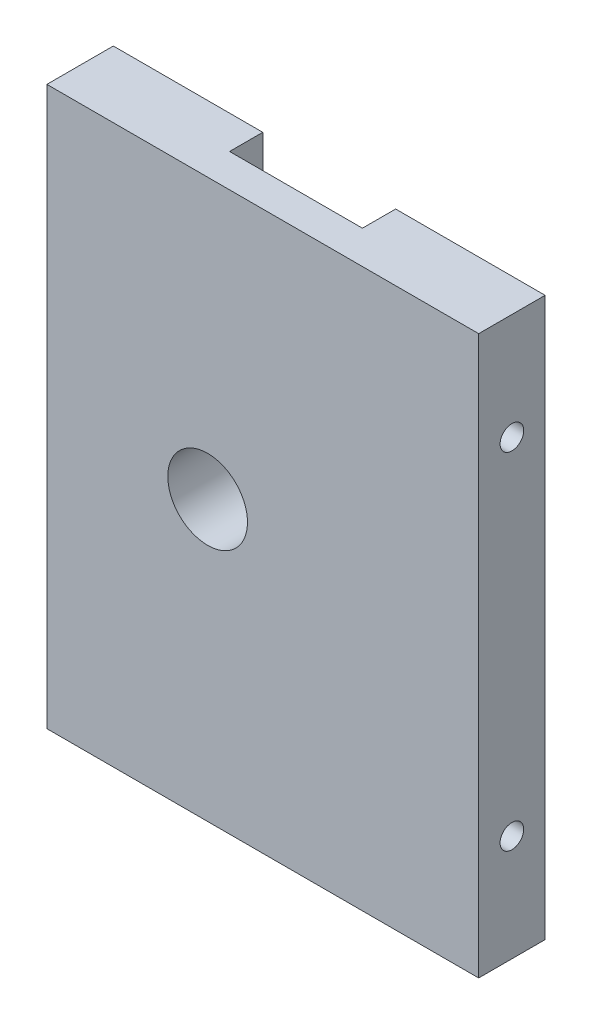
SolidWorks part; units mm, degrees
ref_plane "Front Plane" through (0, 0, 0) normal (0, 0, 1) x (1, 0, 0)
ref_plane "Top Plane" through (0, 0, 0) normal (0, 1, 0) x (1, 0, 0)
ref_plane "Right Plane" through (0, 0, 0) normal (1, 0, 0) x (0, 0, -1)
sketch "Sketch1" plane through (0, 0, 0) normal (0, 0, 1) x (1, 0, 0)
  line L1 (0, 0) -> (32.5, 0)
  line L2 (0, 0) -> (0, 42)
  line L3 (0, 42) -> (32.5, 42)
  line L4 (32.5, 0) -> (32.5, 42)
extrude "Boss-Extrude2" add sketch "Sketch1" along normal blind 5
sketch "Sketch2" plane through (0, 0, 5) normal (0, 0, 1) x (1, 0, 0)
  line L0 (0, 42) -> (0, 34)
  line L1 (0, 42) -> (0, 0) construction
  line L2 (0, 34) -> (32.5, 34)
  line L3 (32.5, 0) -> (32.5, 42) construction
  line L4 (0, 0) -> (0, 8)
  line L5 (0, 8) -> (32.5, 8)
sketch "Sketch3" plane through (0, 0, 0) normal (-1, 0, 0) x (0, 0, 1)
  line L0 (5, 34) -> (0, 34)
  line L1 (5, 42) -> (5, 34) construction
  line L2 (0, 42) -> (0, 0) construction
  line L3 (5, 8) -> (0, 8)
  line L4 (5, 0) -> (5, 8) construction
  line L5 (5, 42) -> (5, 0) construction
hole_wizard "#2-56 Tapped Hole1" positions "Sketch4" profile "Sketch5" tap size "#2-56" standard "ANSI Inch"
sketch "Sketch4" plane through (0, 0, 0) normal (-1, 0, 0) x (0, 0, 1)
  line L0 (5, 34) -> (0, 34) construction
  line L1 (5, 8) -> (0, 8) construction
  point P0 (2.5, 34)
  point P4 (2.5, 8)
sketch "Sketch5" plane through (0, 34, 2.5) normal (0, 1, 0) x (0, 0, 1)
  line L0 (0, 0) -> (0, 8)
  line L1 (0, 8) -> (0.889, 7.4658)
  line L2 (0.889, 7.4658) -> (0.889, 0)
  line L5 (0.889, 0) -> (0, 0)
  line L10 (0, 8) -> (-0.889, 7.4658) construction
  line L11 (0, -6.35) -> (0, 107.95) construction
  dimension "Tap Drill Dia." = 1.778
  dimension "Tap Drill Depth" = 8
  dimension "Drill Angle" = 118
cosmetic thread "Hole Thread1" parameters "D1"=4.37, "D2"=2.1844
cosmetic thread "Hole Thread2" parameters "D1"=4.37, "D2"=2.1844
sketch "Sketch6" plane through (32.5, 0, 0) normal (1, 0, 0) x (0, 0, -1)
  line L0 (-5, 34) -> (0, 34)
  line L1 (-5, 8) -> (0, 8)
hole_wizard "#2-56 Tapped Hole2" positions "Sketch7" profile "Sketch8" tap size "#2-56" standard "ANSI Inch"
sketch "Sketch7" plane through (32.5, 0, 0) normal (1, 0, 0) x (0, 0, -1)
  point P0 (-2.5, 34)
  point P3 (-2.5, 8)
sketch "Sketch8" plane through (32.5, 34, 2.5) normal (0, 1, 0) x (0, 0, -1)
  line L0 (0, 0) -> (0, 8)
  line L1 (0, 8) -> (0.889, 7.4658)
  line L2 (0.889, 7.4658) -> (0.889, 0)
  line L5 (0.889, 0) -> (0, 0)
  line L10 (0, 8) -> (-0.889, 7.4658) construction
  line L11 (0, -6.35) -> (0, 107.95) construction
  dimension "Tap Drill Dia." = 1.778
  dimension "Tap Drill Depth" = 8
  dimension "Drill Angle" = 118
cosmetic thread "Hole Thread3" parameters "D1"=4.37, "D2"=2.1844
cosmetic thread "Hole Thread4" parameters "D1"=4.37, "D2"=2.1844
sketch "Sketch9" plane through (0, 0, 0) normal (0, 0, -1) x (-1, 0, 0)
  line L0 (0, 21) -> (-32.5, 21)
  line L1 (0, 42) -> (0, 0) construction
  line L2 (-32.5, 0) -> (-32.5, 42) construction
  line L3 (-16.25, 21) -> (-12.1, 21)
  circle A0 centre (-12.1, 21) radius 3
  point P9 (-9.5953, 21)
extrude "Cut-Extrude1" cut sketch "Sketch9" against normal blind 5 contours L0 A0 | L0 A0
sketch "Sketch10" plane through (0, 0, 0) normal (0, 0, -1) x (-1, 0, 0)
  line L0 (-32.5, 42) -> (-21.25, 42)
  line L1 (-32.5, 42) -> (0, 42) construction
  line L2 (0, 42) -> (-11.25, 42)
  line L3 (-11.25, 42) -> (-11.25, 35.5)
  line L4 (-11.25, 35.5) -> (-21.25, 35.5)
  line L5 (-21.25, 35.5) -> (-21.25, 42)
  line L7 (-21.25, 42) -> (-11.25, 42)
  line L8 (-21.25, 42) -> (-21.25, 35.5)
  line L9 (-21.25, 35.5) -> (-11.25, 35.5)
  line L10 (-11.25, 42) -> (-11.25, 35.5)
  line M4 (0, 42) -> (-32.5, 42)
extrude "Cut-Extrude2" cut sketch "Sketch10" against normal blind 2.5 contours L5 L4 L3 M4
